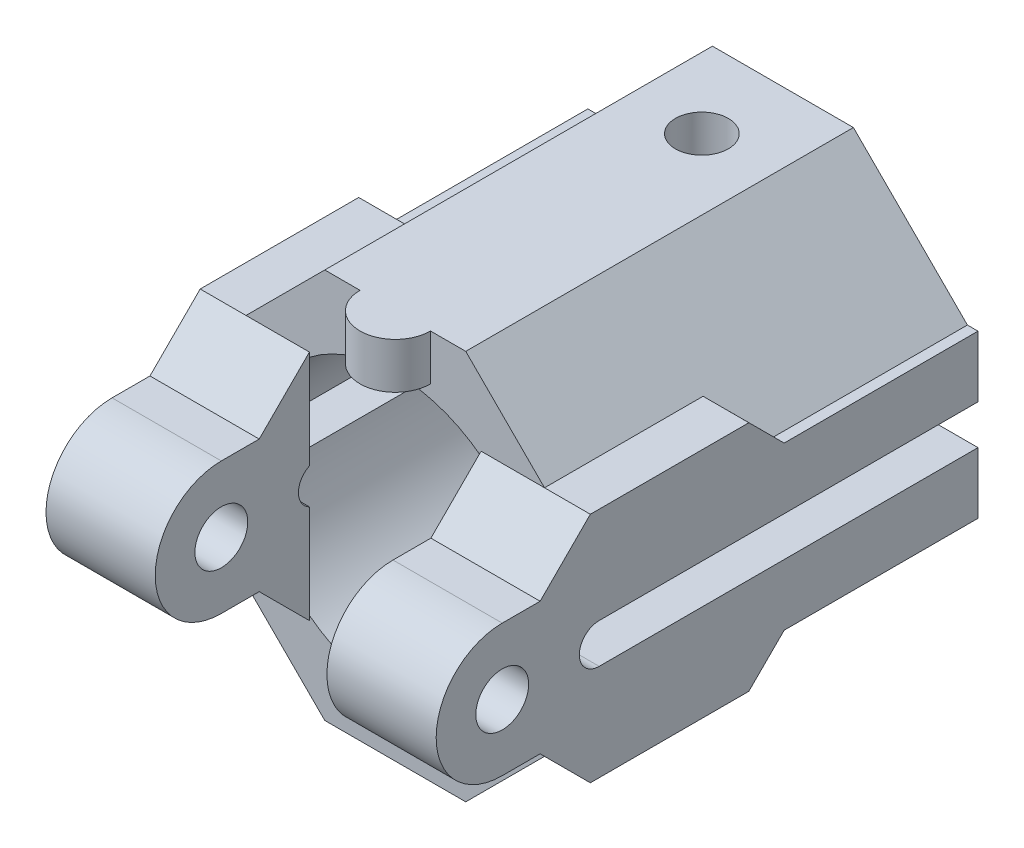
SolidWorks part; units mm, degrees
ref_plane "Front Plane" through (0, 0, 0) normal (0, 0, 1) x (1, 0, 0)
ref_plane "Top Plane" through (0, 0, 0) normal (0, 1, 0) x (1, 0, 0)
ref_plane "Right Plane" through (0, 0, 0) normal (1, 0, 0) x (0, 0, -1)
sketch "Sketch1" plane through (0, 0, 0) normal (0, 0, 1) x (1, 0, 0)
  line L0 (-11.0711, 4) -> (-11.0711, -4)
  line L1 (11.0711, 4) -> (11.0711, -4)
  line L2 (-4, -11.0711) -> (4, -11.0711)
  line L3 (-4, 11.0711) -> (4, 11.0711)
  line L4 (-1000, 0) -> (49000, 0) construction
  line L5 (0, -1000) -> (0, 49000) construction
  line L6 (-11.0711, -4) -> (-4, -11.0711)
  line L7 (-11.0711, 4) -> (-4, 11.0711)
  line L8 (4, 11.0711) -> (11.0711, 4)
  line L9 (11.0711, -4) -> (4, -11.0711)
  circle A0 centre (0, 0) radius 8
  dimension "D1" = 16
  dimension "D2" = 4
  dimension "D3" = 8
  dimension "D4" = 8
  dimension "D5" = 4
  dimension "D6" = 8
  dimension "D7" = 4
  dimension "D8" = 8
  dimension "D9" = 4
  dimension "D10" = 45
  dimension "D11" = 10
  dimension "D12" = 45
  dimension "D13" = 45
extrude "Boss-Extrude1" add sketch "Sketch1" along normal blind 22
sketch "Sketch2" plane through (11.0711, 0, 0) normal (1, 0, 0) x (0, 0, -1)
  line L0 (0, -4) -> (0, 4) construction
  line L1 (0, -4.6) -> (-11, -4.6)
  line L2 (0, -4.6) -> (0, 4.6)
  line L3 (0, 4.6) -> (-11, 4.6)
  line L4 (-11, -4.6) -> (-11, 4.6) construction
  line L5 (-11, -4.6) -> (-13.0058, -6.6)
  line L6 (-11, 6.6) -> (-30, 6.6) construction
  line L7 (-11, 6.6) -> (-11, -6.6) construction
  line L8 (-11, -6.6) -> (-30, -6.6) construction
  line L9 (-30, 6.6) -> (-30, -6.6) construction
  line L10 (-11, 4.6) -> (-13.0029, 6.6)
  line L11 (-22, 6.6) -> (-24.85, 3.75)
  line L12 (-13.0058, 4.6) -> (-22.0058, 4.6) construction
  line L13 (-11, 4.6) -> (-11, -4.6) construction
  line L14 (-13.0058, 4.6) -> (-13.0058, -4.6) construction
  line L15 (-13.0058, -4.6) -> (-22.0058, -4.6) construction
  line L16 (-22.0058, 4.6) -> (-22.0058, -4.6) construction
  line L17 (-22, 4) -> (-22, 11.0711) construction
  line L18 (-22, -6.6) -> (-24.85, -3.75)
  line L19 (-22, -11.0711) -> (-22, -4) construction
  line L20 (-1000, 0) -> (49000, 0) construction
  line L21 (-27, 3.75) -> (-22.0058, 3.75)
  line L22 (-27, -3.75) -> (-22.0058, -3.75)
  line L23 (-22, -6.6) -> (-13.0058, -6.6)
  line L24 (-22, 6.6) -> (-13.0029, 6.6)
  circle A0 centre (-27, 0) radius 3.75
  circle A1 centre (-27, 0) radius 1.5
  dimension "D17" = 3
  dimension "D18" = 7.5
  dimension "D1" = 11
  dimension "D2" = 9.2
  dimension "D3" = 4.6
  dimension "D4" = 19
  dimension "D5" = 0
  dimension "D6" = 13.2
  dimension "D7" = 6.6
  dimension "D8" = 9
  dimension "D9" = 0
  dimension "D10" = 4.6
  dimension "D11" = 9.2
  dimension "D12" = 0
  dimension "D13" = 45
  dimension "D14" = 45
  dimension "D15" = 0
  dimension "D16" = 0
  dimension "D19" = 27
extrude "Boss-Extrude3" add sketch "Sketch2" against normal blind 6.2
sketch "Sketch6" plane through (-11.0711, 0, 0) normal (-1, 0, 0) x (0, 0, 1)
  line L0 (11, -4.7491) -> (0, -4.7491)
  line L1 (0, -4.7491) -> (0, 4.4509)
  line L2 (11, 4.4509) -> (0, 4.4509)
  line L22 (0, 11.0711) -> (0, 4) construction
  line L23 (22.0058, 4.6) -> (22.0058, -4.6) construction
  line L24 (13.0058, -4.6) -> (22.0058, -4.6) construction
  line L25 (13.0058, 4.6) -> (13.0058, -4.6) construction
  line L26 (11, 4.4509) -> (11, -4.7491) construction
  line L27 (13.0058, 4.6) -> (22.0058, 4.6) construction
  line L28 (30, 6.6) -> (30, -6.6) construction
  line L29 (11, -6.6) -> (30, -6.6) construction
  line L30 (11, 6.6) -> (11, -6.6) construction
  line L31 (11, 6.6) -> (30, 6.6) construction
  line L32 (11, -4.7491) -> (11, 4.4509) construction
  line L33 (22, 6.6) -> (13.0029, 6.6)
  line L34 (22, -6.6) -> (13.0058, -6.6)
  line L35 (27, -3.75) -> (22.0058, -3.75)
  line L36 (27, 3.75) -> (22.0058, 3.75)
  line L37 (22, -6.6) -> (24.85, -3.75)
  line L38 (22, 6.6) -> (24.85, 3.75)
  line L39 (11, 4.4509) -> (13.0029, 6.6)
  line L40 (11, -4.7491) -> (13.0058, -6.6)
  circle A2 centre (27, 0) radius 1.5
  circle A3 centre (27, 0) radius 3.75
  dimension "D2" = 9.2
extrude "Boss-Extrude4" add sketch "Sketch6" against normal blind 6.2
sketch "Sketch7" plane through (11.0711, 0, 0) normal (1, 0, 0) x (0, 0, -1)
  line L0 (0, -4.6) -> (0, 4.6) construction
  line L1 (0, 1.125) -> (-21.5, 1.125)
  line L2 (0, 1.125) -> (0, -1.125)
  line L3 (0, -1.125) -> (-21.5, -1.125)
  line L4 (-21.5, 1.125) -> (-21.5, -1.125)
  circle A0 centre (-21.5, 0) radius 1.125
  line M4 (0, -4.6) -> (0, 4.6)
  dimension "D1" = 21.5
  dimension "D2" = 1.125
  dimension "D3" = 2.25
extrude "Cut-Extrude2" cut sketch "Sketch7" against normal blind 30 contours A0 L3 L1 M4 | L4 A0 | L4 A0
sketch "Sketch8" plane through (0, 11.0711, 0) normal (0, 1, 0) x (1, 0, 0)
  circle A0 centre (0, -4.6) radius 1.5
  dimension "D1" = 3
  dimension "D2" = 4.6
extrude "Cut-Extrude3" cut sketch "Sketch8" against normal blind 30
sketch "Sketch9" plane through (0, 0, 0) normal (0, 0, -1) x (-1, 0, 0)
  circle A0 centre (0, 0) radius 8
extrude "Cut-Extrude4" cut sketch "Sketch9" against normal blind 22
sketch "Sketch10" plane through (0, 11.0711, 0) normal (0, 1, 0) x (1, 0, 0)
  line L0 (0, -1000) -> (0, 49000) construction
  line L1 (4, -22) -> (-4, -22) construction
  circle A0 centre (0, -22) radius 2
  dimension "D1" = 4
extrude "Boss-Extrude5" add sketch "Sketch10" against normal blind 2.6
